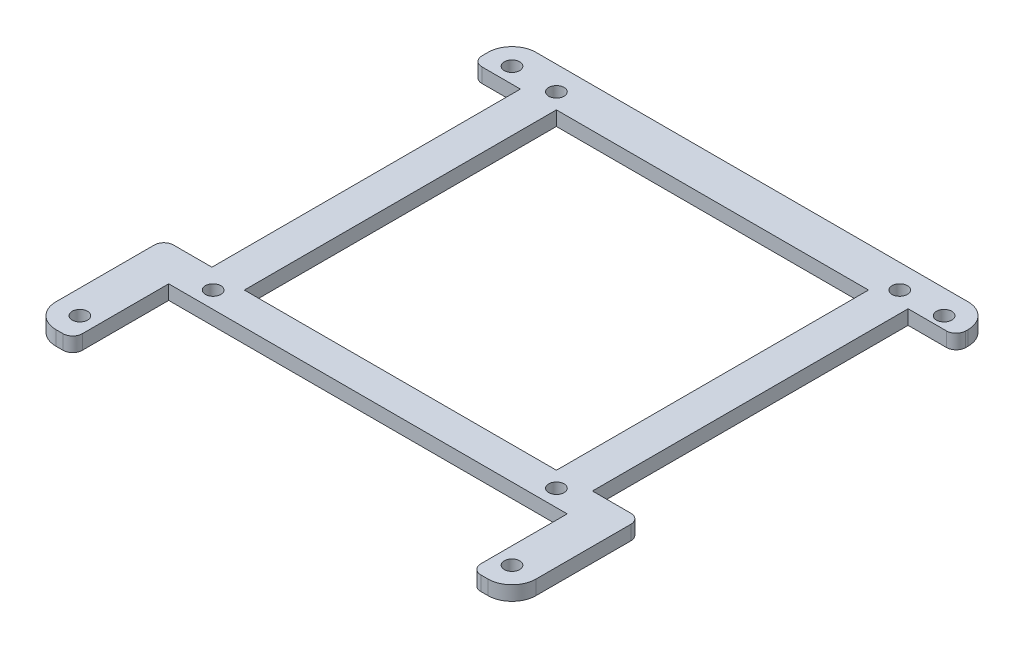
SolidWorks part; units mm, degrees
ref_plane "Front Plane" through (0, 0, 0) normal (0, 0, 1) x (1, 0, 0)
ref_plane "Top Plane" through (0, 0, 0) normal (0, 1, 0) x (1, 0, 0)
ref_plane "Right Plane" through (0, 0, 0) normal (1, 0, 0) x (0, 0, -1)
sketch "Sketch1" plane through (0, 0, 0) normal (0, 1, 0) x (1, 0, 0)
  line L0 (-50, 41.75) -> (-40, 41.75)
  line L1 (-50, -50) -> (50, -50)
  line L2 (-50, -50) -> (-50, 50)
  line L3 (-50, 50) -> (50, 50)
  line L4 (50, -50) -> (50, 50)
  line L5 (0, 50) -> (0, -50) construction
  line L6 (-50, 0) -> (50, 0) construction
  line L7 (45, -45) -> (-45, -45) construction
  line L8 (45, -45) -> (45, 45) construction
  line L9 (45, 45) -> (-45, 45) construction
  line L10 (-45, -45) -> (-45, 45) construction
  line L11 (0, 45) -> (0, -45) construction
  line L12 (45, 0) -> (-45, 0) construction
  line L13 (35.75, -26.5) -> (-35.75, -26.5) construction
  line L14 (35.75, -26.5) -> (35.75, 45) construction
  line L15 (35.75, 45) -> (-35.75, 45) construction
  line L16 (-35.75, -26.5) -> (-35.75, 45) construction
  line L17 (0, 45) -> (0, -26.5) construction
  line L18 (35.75, 9.25) -> (-35.75, 9.25) construction
  line L19 (-41.5, -30) -> (41.5, -30)
  line L20 (-41.5, -30) -> (-41.5, -50)
  line L21 (-41.5, -50) -> (41.5, -50)
  line L22 (41.5, -30) -> (41.5, -50)
  line L23 (0, -50) -> (0, -30) construction
  line L24 (-41.5, -40) -> (41.5, -40) construction
  line L25 (-32.5, 41.75) -> (32.5, 41.75)
  line L26 (-32.5, 41.75) -> (-32.5, -23.25)
  line L27 (-32.5, -23.25) -> (32.5, -23.25)
  line L28 (32.5, 41.75) -> (32.5, -23.25)
  line L29 (0, -23.25) -> (0, 41.75) construction
  line L30 (-32.5, 9.25) -> (32.5, 9.25) construction
  line L31 (-40, 41.75) -> (-40, -22.5)
  line L32 (-40, -22.5) -> (-50, -22.5)
  line L33 (50, -23.25) -> (40, -23.25)
  line L34 (40, -23.25) -> (40, 42.5)
  line L35 (40, 42.5) -> (50, 42.5)
  circle A0 centre (-45, 45) radius 1.6
  circle A1 centre (45, 45) radius 1.6
  circle A2 centre (45, -45) radius 1.6
  circle A3 centre (-45, -45) radius 1.6
  circle A4 centre (-35.75, 45) radius 1.6
  circle A5 centre (35.75, 45) radius 1.6
  circle A6 centre (35.75, -26.5) radius 1.6
  circle A7 centre (-35.75, -26.5) radius 1.6
  point P0 (0, 0)
  point P4 (0, 0)
  point P18 (0, 9.25)
  point P29 (0, -40)
  point P33 (0, 9.25)
  dimension "D5" = 3.2
  dimension "D6" = 3.2
  dimension "D1" = 100
  dimension "D2" = 100
  dimension "D3" = 90
  dimension "D4" = 90
  dimension "D7" = 71.5
  dimension "D8" = 71.5
  dimension "D9" = 20
  dimension "D10" = 83
  dimension "D11" = 65
  dimension "D12" = 65
  dimension "D13" = 10
  dimension "D14" = 10
extrude "Boss-Extrude1" add sketch "Sketch1" along normal blind 3 contours L34 L35 L4 L3 L2 L0 L31 L32 L1 L20 L19 L22 L33 A7 A6 A5 A4 A3 A2 A1 A0 L25 L28 L27 L26
fillet "Fillet1" radius 2 6 edges at (-50, 1.5, -41.75) (-50, 1.5, 22.5) (-41.5, 1.5, 50) (41.5, 1.5, 50) (50, 1.5, 23.25) (50, 1.5, -42.5)
fillet "Fillet2" radius 5 4 edges at (-50, 1.5, 50) (50, 1.5, 50) (50, 1.5, -50) (-50, 1.5, -50)
